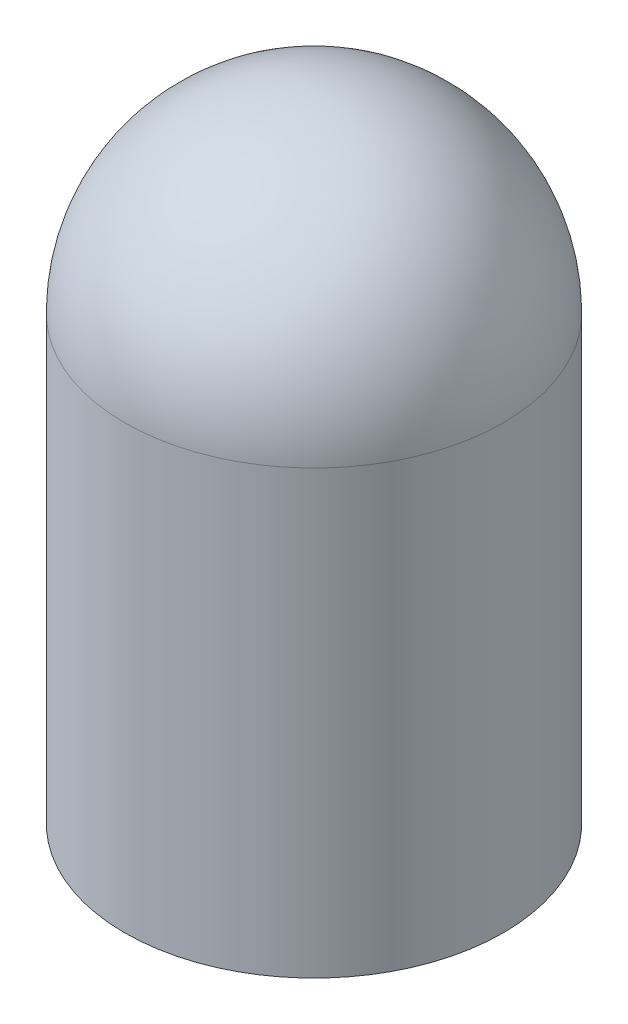
SolidWorks part; units mm, degrees
ref_plane "Front Plane" through (0, 0, 0) normal (0, 0, 1) x (1, 0, 0)
ref_plane "Top Plane" through (0, 0, 0) normal (0, 1, 0) x (1, 0, 0)
ref_plane "Right Plane" through (0, 0, 0) normal (1, 0, 0) x (0, 0, -1)
sketch "Sketch2" plane through (0, 0, 0) normal (0, 0, 1) x (1, 0, 0)
  line L0 (30, 70) -> (30, 0)
  line L2 (0, 100) -> (0, 0)
  line L3 (0, 0) -> (30, 0)
  arc A0 (0, 100) -> (30, 70) centre (0, 70) cw
  dimension "D3" = 30
  dimension "D1" = 30
  dimension "D2" = 100
  dimension "D4" = 90
revolve "Revolve1" add sketch "Sketch2" angle 360 about L2
